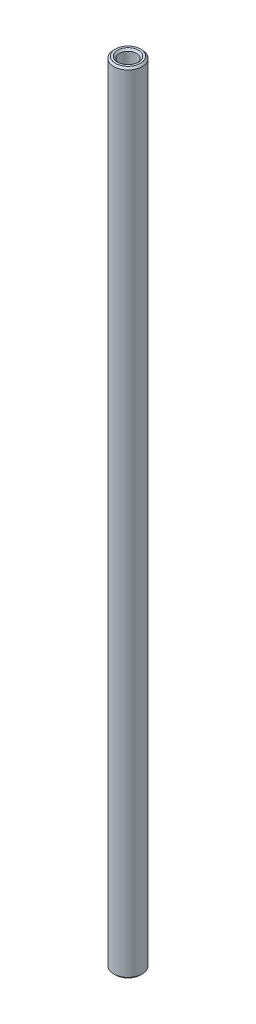
SolidWorks part; units mm, degrees
ref_plane "Front Plane" through (0, 0, 0) normal (0, 0, 1) x (1, 0, 0)
ref_plane "Top Plane" through (0, 0, 0) normal (0, 1, 0) x (1, 0, 0)
ref_plane "Right Plane" through (0, 0, 0) normal (1, 0, 0) x (0, 0, -1)
sketch "Sketch1" plane through (0, 0, 0) normal (0, 1, 0) x (1, 0, 0)
  circle A0 centre (0, 0) radius 1.9844
  circle A1 centre (0, 0) radius 1.1906
  dimension "D1" = 3.9688
  dimension "D2" = 0.7937
extrude "Boss-Extrude1" add sketch "Sketch1" along normal mid plane 109.5375
chamfer "Chamfer1" distance 0.254 angle 45 4 edges at (0, -54.7687, 1.1906) (0, -54.7687, 1.9844) (0, 54.7687, 1.1906) (0, 54.7687, 1.9844)
